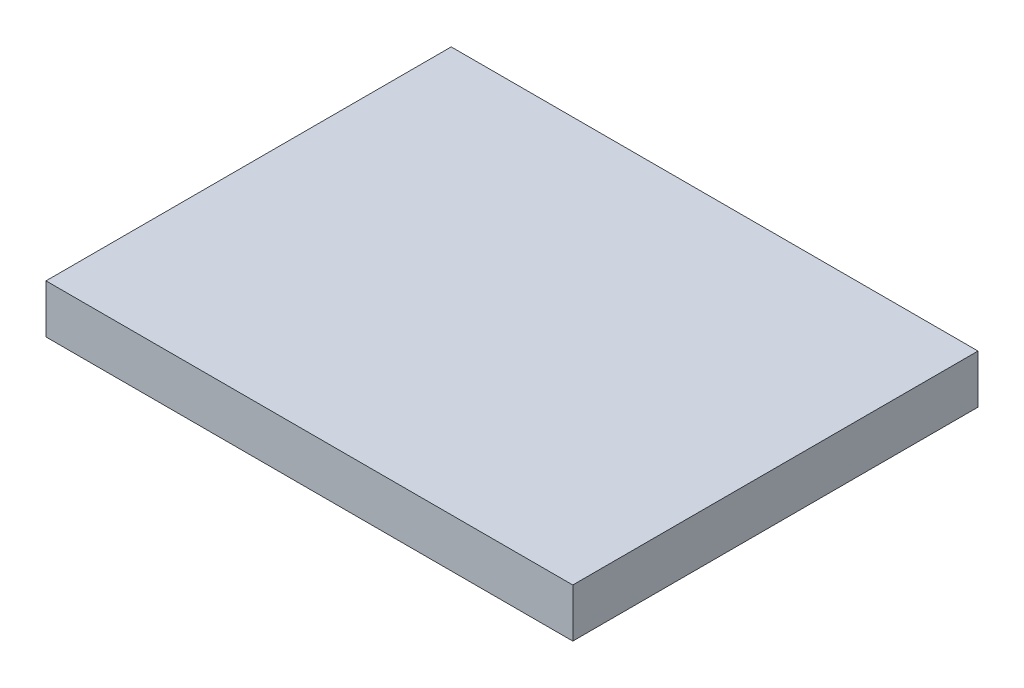
SolidWorks part; units mm, degrees
ref_plane "Front" through (0, 0, 0) normal (0, 0, 1) x (1, 0, 0)
ref_plane "Top" through (0, 0, 0) normal (0, 1, 0) x (1, 0, 0)
ref_plane "Right" through (0, 0, 0) normal (1, 0, 0) x (0, 0, -1)
sketch "Sketch1" plane through (0, 0, 0) normal (0, 1, 0) x (1, 0, 0)
  line L1 (0, 0) -> (130, 0)
  line L2 (0, 0) -> (0, 100)
  line L3 (0, 100) -> (130, 100)
  line L4 (130, 0) -> (130, 100)
extrude "Boss-Extrude1" add sketch "Sketch1" along normal blind 12
